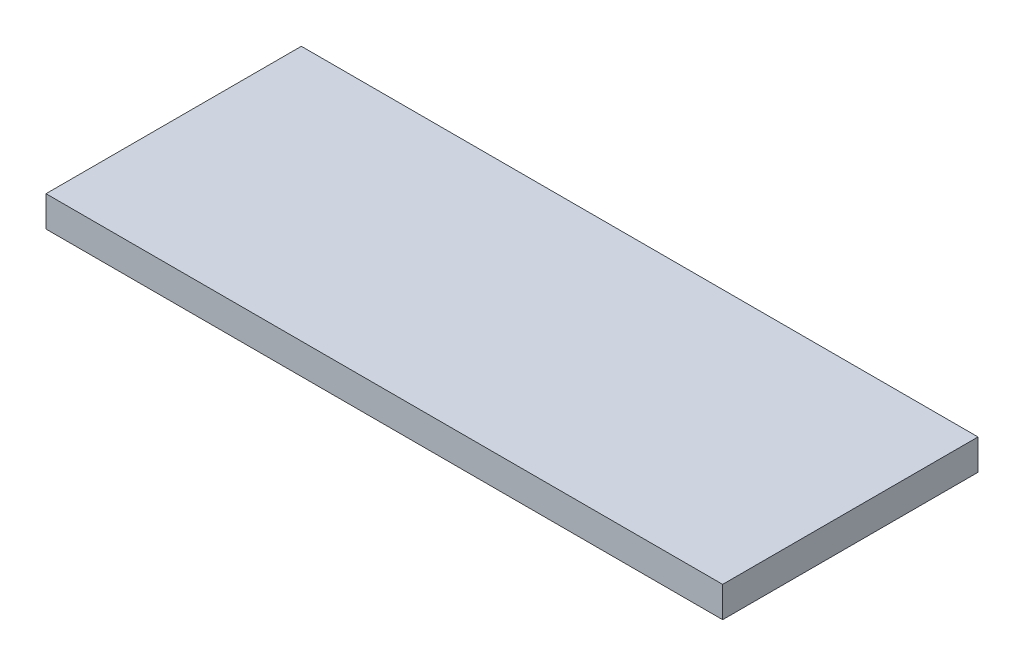
SolidWorks part; units mm, degrees
material "Maple"
ref_plane "Front Plane" through (0, 0, 0) normal (0, 0, 1) x (1, 0, 0)
ref_plane "Top Plane" through (0, 0, 0) normal (0, 1, 0) x (1, 0, 0)
ref_plane "Right Plane" through (0, 0, 0) normal (1, 0, 0) x (0, 0, -1)
sketch "Sketch1" plane through (0, 0, 0) normal (0, 1, 0) x (1, 0, 0)
  line L0 (66.25, 18) -> (66.25, -18) construction
  line L1 (-66.25, 25) -> (66.25, 25)
  line L2 (-66.25, 25) -> (-66.25, -25)
  line L3 (-66.25, -25) -> (66.25, -25)
  line L4 (66.25, 25) -> (66.25, -25)
  line L5 (-66.25, 25) -> (66.25, -25) construction
  line L6 (-66.25, -25) -> (66.25, 25) construction
  point P0 (0, 0)
  dimension "D2" = 50
extrude "Boss-Extrude1" add sketch "Sketch1" along normal blind 6
ref_plane "Plane1" through (0, 3, 0) normal (0, 1, 0) x (1, 0, 0)
